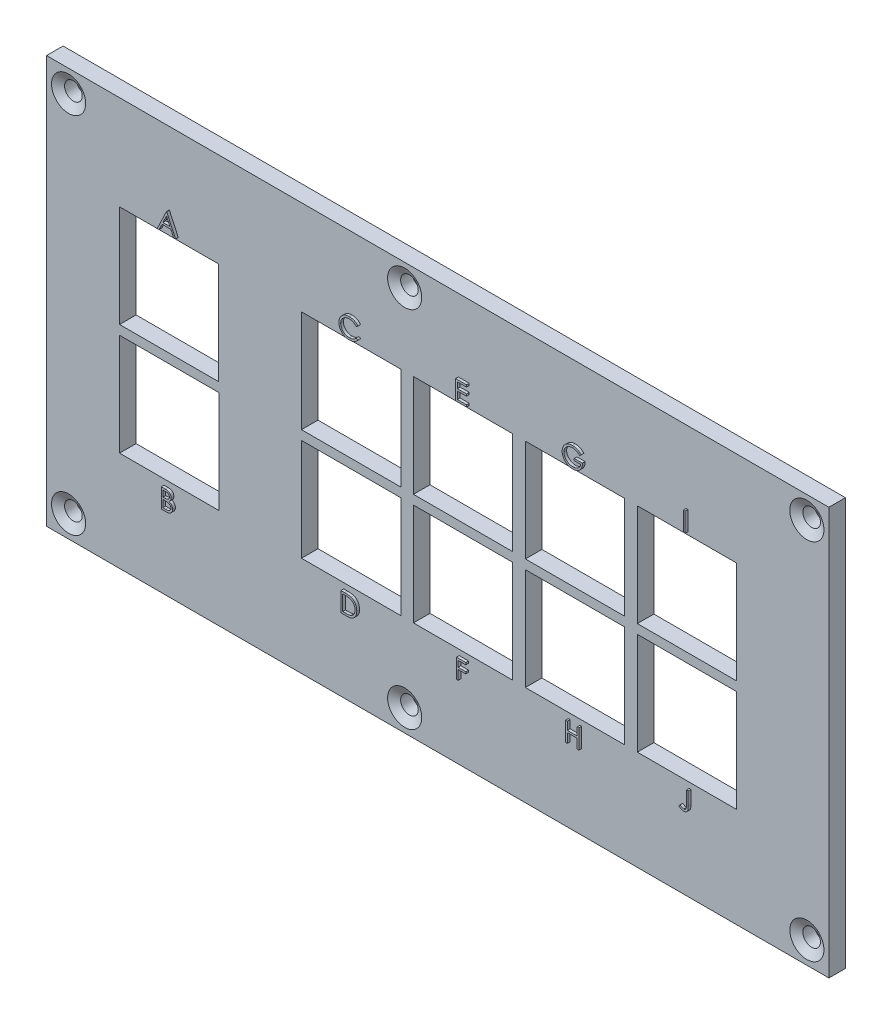
SolidWorks part; units mm, degrees
ref_plane "Plan de face" through (0, 0, 0) normal (0, 0, 1) x (1, 0, 0)
ref_plane "Plan de dessus" through (0, 0, 0) normal (0, 1, 0) x (1, 0, 0)
ref_plane "Plan de droite" through (0, 0, 0) normal (1, 0, 0) x (0, 0, -1)
sketch "Esquisse1" plane through (0, 0, 0) normal (0, 0, 1) x (1, 0, 0)
  line L1 (0, 0) -> (142, 0)
  line L2 (0, 0) -> (0, 74)
  line L3 (0, 74) -> (142, 74)
  line L4 (142, 0) -> (142, 74)
  dimension "D1" = 142
  dimension "D2" = 74
extrude "Boss.-Extru.1" add sketch "Esquisse1" along normal blind 3
sketch "Esquisse2" plane through (0, 0, 3) normal (0, 0, 1) x (1, 0, 0)
  line L1 (0, 74) -> (0, 0) construction
  line L2 (142, 74) -> (0, 74) construction
  line L5 (142, 0) -> (142, 74) construction
  line L6 (0, 0) -> (142, 0) construction
  circle A0 centre (4, 70) radius 1.6
  circle A1 centre (65, 70) radius 1.6
  circle A2 centre (138, 70) radius 1.6
  circle A3 centre (138, 4) radius 1.6
  circle A4 centre (65, 4) radius 1.6
  circle A5 centre (4, 4) radius 1.6
  dimension "D1" = 3.2
  dimension "D4" = 3.2
  dimension "D13" = 3.2
  dimension "D14" = 3.2
  dimension "D15" = 3.2
  dimension "D18" = 3.2
  dimension "D2" = 4
  dimension "D3" = 4
  dimension "D5" = 4
  dimension "D6" = 65
  dimension "D7" = 4
  dimension "D8" = 4
  dimension "D9" = 4
  dimension "D10" = 4
  dimension "D11" = 4
  dimension "D12" = 65
  dimension "D16" = 4
  dimension "D17" = 4
extrude "Enlèv. mat.-Extru.1" cut sketch "Esquisse2" against normal blind 3
chamfer "Chanfrein1" distance 1.5 angle 30 6 edges at (5.6, 4, 3) (66.6, 4, 3) (139.6, 4, 3) (139.6, 70, 3) (66.6, 70, 3) (5.6, 70, 3)
sketch "Esquisse3" plane through (0, 0, 3) normal (0, 0, 1) x (1, 0, 0)
  line L0 (66.588, 56.85) -> (66.588, 38.324)
  line L1 (13.25, 56.85) -> (31.25, 56.85)
  line L2 (13.25, 56.85) -> (13.25, 38.35)
  line L3 (13.25, 38.35) -> (31.25, 38.35)
  line L4 (31.25, 56.85) -> (31.25, 38.35)
  line L5 (46.268, 56.85) -> (64.288, 56.85)
  line L6 (46.268, 56.85) -> (46.268, 38.324)
  line L7 (46.268, 38.324) -> (64.288, 38.324)
  line L8 (0, 74) -> (0, 0) construction
  line L9 (142, 74) -> (0, 74) construction
  line L10 (64.288, 56.85) -> (64.288, 38.324)
  line L11 (13.25, 36.657) -> (31.268, 36.657)
  line L12 (13.25, 36.657) -> (13.25, 18.127)
  line L13 (13.25, 18.127) -> (31.268, 18.127)
  line L14 (31.268, 36.657) -> (31.268, 18.127)
  line L15 (66.588, 56.85) -> (84.608, 56.85)
  line L16 (66.588, 38.324) -> (84.608, 38.324)
  line L17 (84.608, 56.85) -> (84.608, 38.324)
  line L18 (86.908, 56.85) -> (86.908, 38.324)
  line L19 (86.908, 56.85) -> (104.928, 56.85)
  line L20 (86.908, 38.324) -> (104.928, 38.324)
  line L21 (104.928, 56.85) -> (104.928, 38.324)
  line L22 (107.228, 56.85) -> (107.228, 38.324)
  line L23 (107.228, 56.85) -> (125.248, 56.85)
  line L24 (107.228, 38.324) -> (125.248, 38.324)
  line L25 (125.248, 56.85) -> (125.248, 38.324)
  line L26 (66.588, 36.64) -> (66.588, 18.114)
  line L27 (46.268, 36.64) -> (64.288, 36.64)
  line L28 (46.268, 36.64) -> (46.268, 18.114)
  line L29 (46.268, 18.114) -> (64.288, 18.114)
  line L30 (64.288, 36.64) -> (64.288, 18.114)
  line L31 (66.588, 36.64) -> (84.608, 36.64)
  line L32 (66.588, 18.114) -> (84.608, 18.114)
  line L33 (84.608, 36.64) -> (84.608, 18.114)
  line L34 (86.908, 36.64) -> (86.908, 18.114)
  line L35 (86.908, 36.64) -> (104.928, 36.64)
  line L36 (86.908, 18.114) -> (104.928, 18.114)
  line L37 (104.928, 36.64) -> (104.928, 18.114)
  line L38 (107.228, 36.64) -> (107.228, 18.114)
  line L39 (107.228, 36.64) -> (125.248, 36.64)
  line L40 (107.228, 18.114) -> (125.248, 18.114)
  line L41 (125.248, 36.64) -> (125.248, 18.114)
  dimension "D1" = 18
  dimension "D2" = 18.5
  dimension "D3" = 13.25
  dimension "D4" = 17.15
  dimension "D5" = 1.693
  dimension "D6" = 18.53
  dimension "D7" = 18.018
  dimension "D8" = 13.25
  dimension "D9" = 18.02
  dimension "D10" = 18.526
  dimension "D11" = 15.018
  dimension "D12" = 17.15
  dimension "D13" = 4
  dimension "D14" = 2
extrude "Enlèv. mat.-Extru.2" cut sketch "Esquisse3" against normal blind 3
sketch "Esquisse4" plane through (0, 0, 3) normal (0, 0, 1) x (1, 0, 0)
  line L0 (13.25, 57.35) -> (31.25, 57.35) construction
  line L1 (13.25, 56.85) -> (13.25, 38.35) construction
  line L2 (31.25, 56.85) -> (13.25, 56.85) construction
  line L3 (66.588, 57.35) -> (84.608, 57.35) construction
  line L4 (84.608, 56.85) -> (66.588, 56.85) construction
  line L5 (46.268, 57.35) -> (64.288, 57.35) construction
  line L6 (64.288, 56.85) -> (46.268, 56.85) construction
  line L7 (86.908, 57.35) -> (104.928, 57.35) construction
  line L8 (107.228, 57.35) -> (125.248, 57.35) construction
  line L9 (13.25, 13.627) -> (31.268, 13.627) construction
  line L10 (13.25, 18.127) -> (31.268, 18.127) construction
  line L11 (46.268, 13.627) -> (64.288, 13.627) construction
  line L12 (66.588, 13.627) -> (84.608, 13.627) construction
  line L13 (86.908, 13.627) -> (104.928, 13.627) construction
  line L14 (107.228, 13.627) -> (125.248, 13.627) construction
  line L15 (31.25, 38.35) -> (31.25, 56.85) construction
  line L16 (13.25, 36.657) -> (13.25, 18.127) construction
  line L17 (31.268, 18.127) -> (31.268, 36.657) construction
  line L18 (46.268, 56.85) -> (46.268, 38.324) construction
  line L19 (64.288, 38.324) -> (64.288, 56.85) construction
  line L20 (66.588, 56.85) -> (66.588, 38.324) construction
  line L21 (86.908, 56.85) -> (86.908, 38.324) construction
  line L22 (84.608, 38.324) -> (84.608, 56.85) construction
  line L23 (125.248, 38.324) -> (125.248, 56.85) construction
  line L24 (107.228, 56.85) -> (107.228, 38.324) construction
  line L25 (104.928, 38.324) -> (104.928, 56.85) construction
  line L26 (46.268, 36.64) -> (46.268, 18.114) construction
  line L27 (64.288, 18.114) -> (64.288, 36.64) construction
  line L28 (66.588, 36.64) -> (66.588, 18.114) construction
  line L29 (84.608, 18.114) -> (84.608, 36.64) construction
  line L30 (86.908, 36.64) -> (86.908, 18.114) construction
  line L31 (125.248, 18.114) -> (125.248, 36.64) construction
  line L32 (107.228, 36.64) -> (107.228, 18.114) construction
  line L33 (104.928, 18.114) -> (104.928, 36.64) construction
  text T0 "A"
  text T1 "E"
  text T2 "C"
  text T3 "G"
  text T4 "I"
  text T5 "B"
  text T6 "D"
  text T7 "F"
  text T8 "H"
  text T9 "J"
  dimension "D1" = 0.5
  dimension "D2" = 0.5
  dimension "D3" = 0.5
  dimension "D4" = 4.5
  dimension "D5" = 0
  dimension "D6" = 0
  dimension "D7" = 0
  dimension "D8" = 0
  dimension "D9" = 0
  dimension "D10" = 0
  dimension "D11" = 0
  dimension "D12" = 0
  dimension "D13" = 0
  dimension "D14" = 0
  dimension "D15" = 0
  dimension "D16" = 0
  dimension "D17" = 0
  dimension "D18" = 0
  dimension "D19" = 0
  dimension "D20" = 0
  dimension "D21" = 0
  dimension "D22" = 0
  dimension "D23" = 0
  dimension "D24" = 0
extrude "Boss.-Extru.2" add sketch "Esquisse4" along normal blind 0.5 separate body
